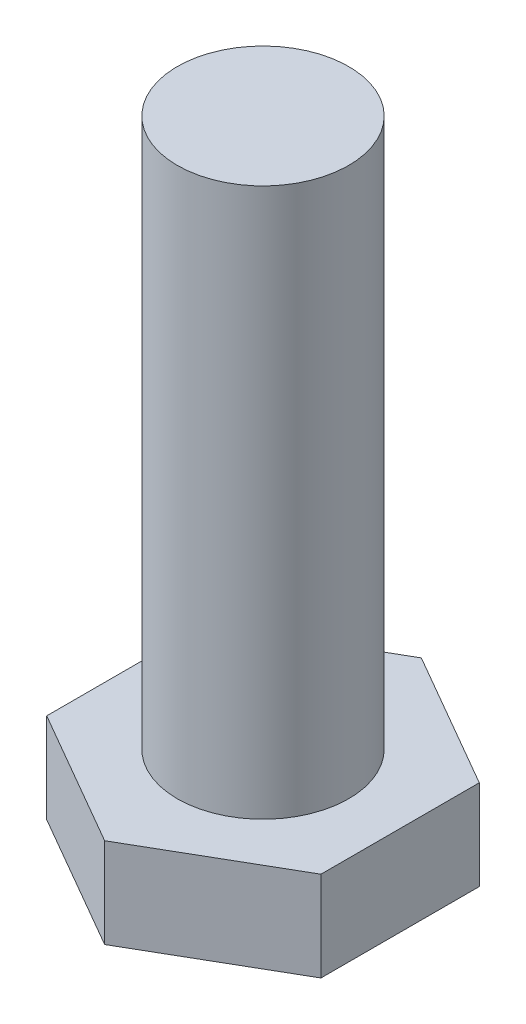
SolidWorks part; units mm, degrees
ref_plane "Спереди" through (0, 0, 0) normal (0, 0, 1) x (1, 0, 0)
ref_plane "Сверху" through (0, 0, 0) normal (0, 1, 0) x (1, 0, 0)
ref_plane "Справа" through (0, 0, 0) normal (1, 0, 0) x (0, 0, -1)
sketch "Эскиз1" plane through (0, 0, 0) normal (0, 1, 0) x (1, 0, 0)
  line L1 (4, -2.3094) -> (4, 2.3094)
  line L2 (4, 2.3094) -> (0, 4.6188)
  line L3 (0, 4.6188) -> (-4, 2.3094)
  line L4 (-4, 2.3094) -> (-4, -2.3094)
  line L5 (-4, -2.3094) -> (0, -4.6188)
  line L6 (0, -4.6188) -> (4, -2.3094)
  circle A0 centre (0, 0) radius 4 construction
extrude "Бобышка-Вытянуть1" add sketch "Эскиз1" along normal blind 3.2
sketch "Эскиз2" plane through (0, 3.2, 0) normal (0, 1, 0) x (1, 0, 0)
  circle A0 centre (0, 0) radius 2.5
extrude "Бобышка-Вытянуть2" add sketch "Эскиз2" along normal blind 16
chamfer "Фаска1" distance 1 angle 30 6 edges at (2, 0, -3.4641) (4, 0, 0) (2, 0, 3.4641) (-2, 0, 3.4641) (-4, 0, 0) (-2, 0, -3.4641)
